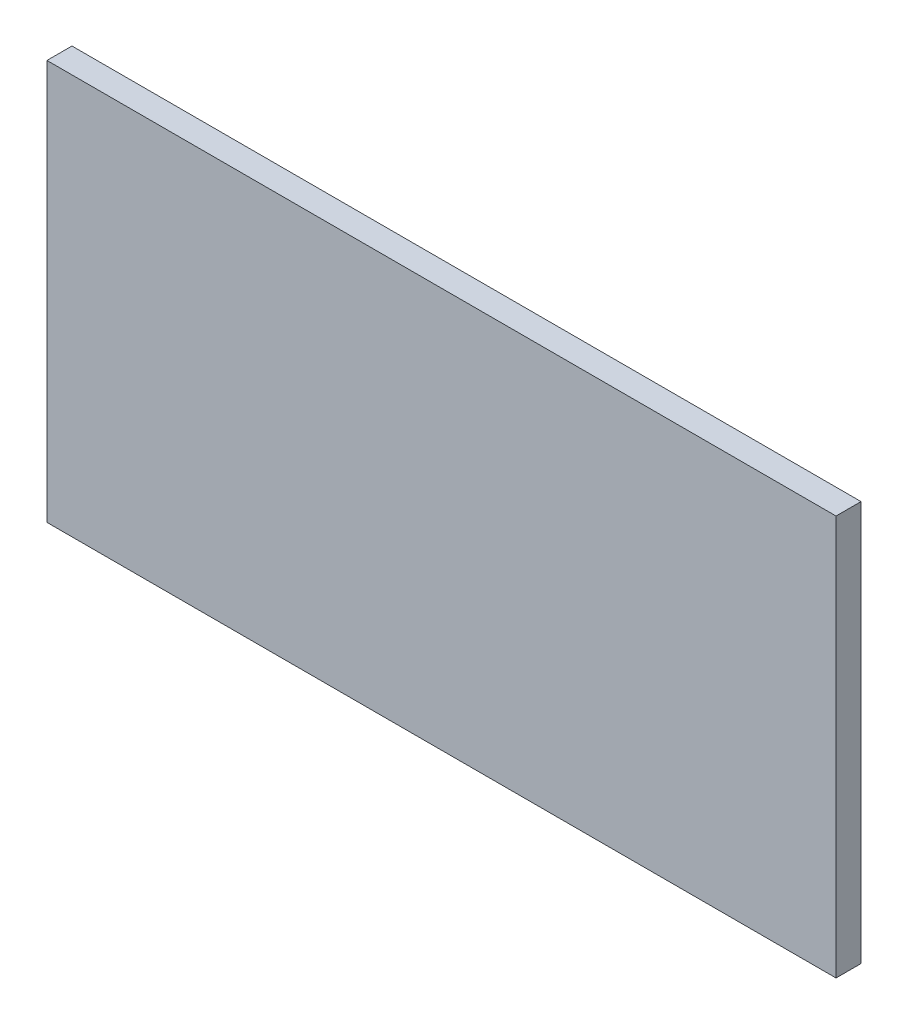
SolidWorks part; units mm, degrees
ref_plane "Front Plane" through (0, 0, 0) normal (0, 0, 1) x (1, 0, 0)
ref_plane "Top Plane" through (0, 0, 0) normal (0, 1, 0) x (1, 0, 0)
ref_plane "Right Plane" through (0, 0, 0) normal (1, 0, 0) x (0, 0, -1)
sketch "Sketch1" plane through (0, 0, 0) normal (0, 0, 1) x (1, 0, 0)
  line L1 (284, -144) -> (-284, -144)
  line L2 (284, -144) -> (284, 144)
  line L3 (284, 144) -> (-284, 144)
  line L4 (-284, -144) -> (-284, 144)
  line L5 (284, -144) -> (-284, 144) construction
  line L6 (284, 144) -> (-284, -144) construction
  point P0 (0, 0)
  dimension "D1" = 288
  dimension "D2" = 568
extrude "Boss-Extrude1" add sketch "Sketch1" along normal blind 18
equation "\"H_DSP\"=18"
equation "\"D1@Boss-Extrude1\"=\"H_DSP\""
